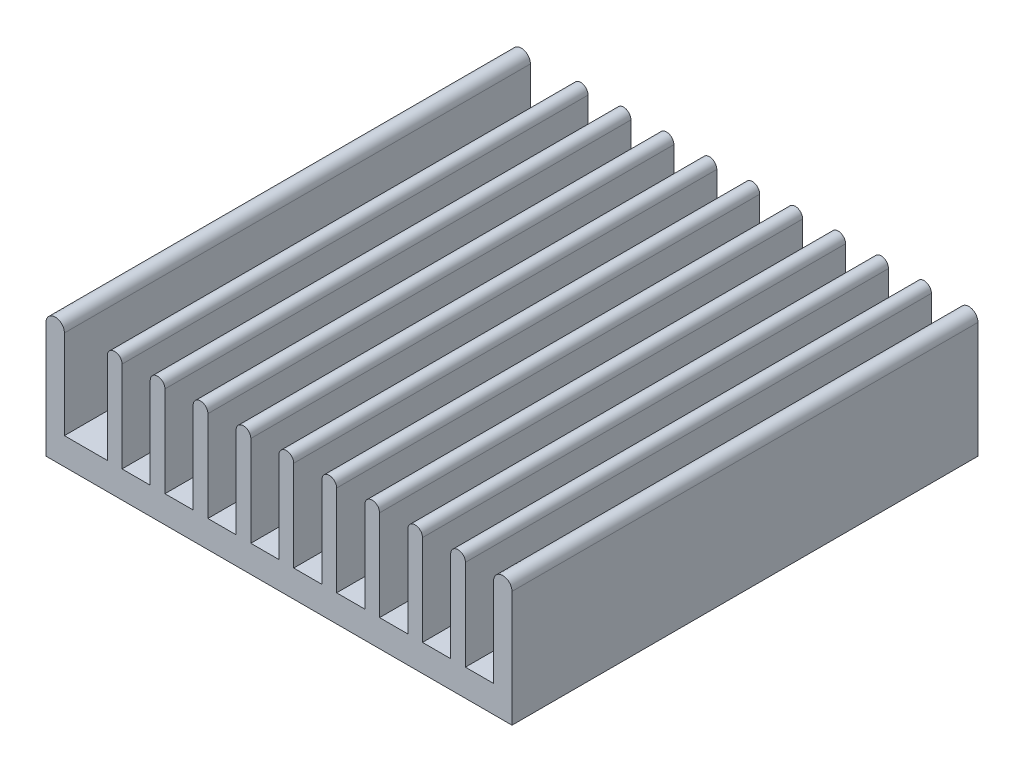
SolidWorks part; units mm, degrees
material "2014-T6"
ref_plane "Front Plane" through (0, 0, 0) normal (0, 0, 1) x (1, 0, 0)
ref_plane "Top Plane" through (0, 0, 0) normal (0, 1, 0) x (1, 0, 0)
ref_plane "Right Plane" through (0, 0, 0) normal (1, 0, 0) x (0, 0, -1)
sketch "Sketch1" plane through (0, 0, 0) normal (0, 0, 1) x (1, 0, 0)
  line L0 (19.0009, 10.2) -> (-9.1991, 10.2) construction
  line L1 (-19, 0) -> (19, 0)
  line L2 (-19, 0) -> (-19, 2.2)
  line L3 (11.7, 2.2) -> (11.7, 9.6)
  line L4 (19, 0) -> (19, 2.2)
  line L5 (15.2, 2.2) -> (17.5, 2.2)
  line L6 (19, 2.2) -> (19, 9.45)
  line L7 (15.2, 2.2) -> (15.2, 9.6)
  line L8 (17.5, 2.2) -> (17.5, 9.45)
  line L9 (14, 9.6) -> (14, 2.2)
  line L10 (10.5, 9.6) -> (10.5, 2.2)
  line L11 (11.7, 2.2) -> (14, 2.2)
  line L12 (8.2, 2.2) -> (8.2, 9.6)
  line L13 (7, 9.6) -> (7, 2.2)
  line L14 (8.2, 2.2) -> (10.5, 2.2)
  line L15 (4.7, 2.2) -> (4.7, 9.6)
  line L16 (3.5, 9.6) -> (3.5, 2.2)
  line L17 (4.7, 2.2) -> (7, 2.2)
  line L18 (1.2, 2.2) -> (1.2, 9.6)
  line L19 (0, 9.6) -> (0, 2.2)
  line L20 (-19, 2.2) -> (-19, 9.45)
  line L21 (-17.5, 9.45) -> (-17.5, 2.2)
  line L22 (1.2, 2.2) -> (3.5, 2.2)
  line L23 (-2.3, 2.2) -> (-2.3, 9.6)
  line L24 (-3.5, 9.6) -> (-3.5, 2.2)
  line L25 (-2.3, 2.2) -> (0, 2.2)
  line L26 (-5.8, 2.2) -> (-5.8, 9.6)
  line L27 (-7, 9.6) -> (-7, 2.2)
  line L28 (-5.8, 2.2) -> (-3.5, 2.2)
  line L29 (-9.3, 2.2) -> (-9.3, 9.6)
  line L30 (-10.5, 9.6) -> (-10.5, 2.2)
  line L31 (-9.3, 2.2) -> (-7, 2.2)
  line L32 (-12.8, 2.2) -> (-12.8, 9.6)
  line L33 (-14, 9.6) -> (-14, 2.2)
  line L34 (-12.8, 2.2) -> (-10.5, 2.2)
  line L35 (-14, 2.2) -> (-17.5, 2.2)
  arc A0 (17.5, 9.45) -> (19, 9.45) centre (18.25, 9.45) cw
  arc A1 (15.2, 9.6) -> (14, 9.6) centre (14.6, 9.6) ccw
  arc A2 (11.7, 9.6) -> (10.5, 9.6) centre (11.1, 9.6) ccw
  arc A3 (8.2, 9.6) -> (7, 9.6) centre (7.6, 9.6) ccw
  arc A4 (4.7, 9.6) -> (3.5, 9.6) centre (4.1, 9.6) ccw
  arc A5 (1.2, 9.6) -> (0, 9.6) centre (0.6, 9.6) ccw
  arc A6 (-2.3, 9.6) -> (-3.5, 9.6) centre (-2.9, 9.6) ccw
  arc A7 (-19, 9.45) -> (-17.5, 9.45) centre (-18.25, 9.45) cw
  arc A8 (-5.8, 9.6) -> (-7, 9.6) centre (-6.4, 9.6) ccw
  arc A9 (-9.3, 9.6) -> (-10.5, 9.6) centre (-9.9, 9.6) ccw
  arc A10 (-12.8, 9.6) -> (-14, 9.6) centre (-13.4, 9.6) ccw
  dimension "D1" = 38
  dimension "D2" = 2.2
  dimension "D3" = 1.5
  dimension "D4" = 9
  dimension "D5" = 1.2
  dimension "D6" = 2.3
  dimension "D7" = 1.5
extrude "Extrude1" add sketch "Sketch1" along normal blind 38
